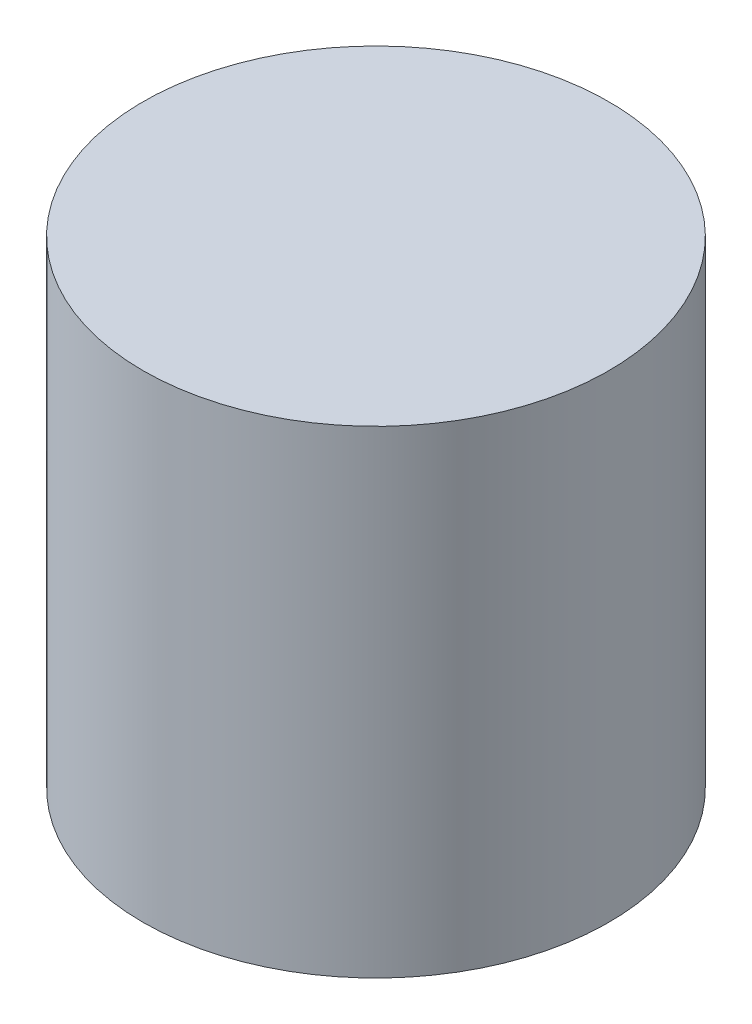
SolidWorks part; units mm, degrees
ref_plane "Front Plane" through (0, 0, 0) normal (0, 0, 1) x (1, 0, 0)
ref_plane "Top Plane" through (0, 0, 0) normal (0, 1, 0) x (1, 0, 0)
ref_plane "Right Plane" through (0, 0, 0) normal (1, 0, 0) x (0, 0, -1)
sketch "Sketch1" plane through (0, 0, 0) normal (0, 1, 0) x (1, 0, 0)
  circle A0 centre (0, 0) radius 9.75
  dimension "D1" = 19.5
extrude "Boss-Extrude1" add sketch "Sketch1" along normal blind 20
